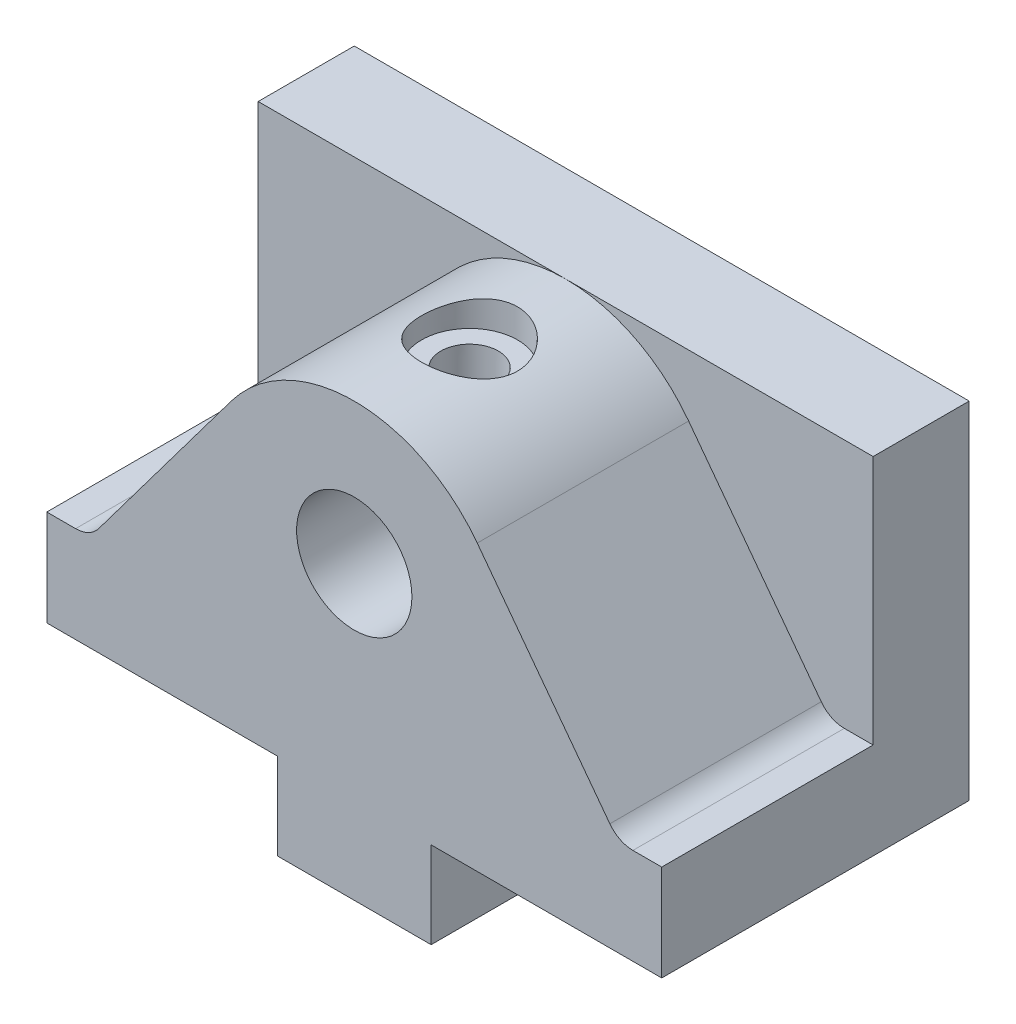
SolidWorks part; units mm, degrees
ref_plane "Front Plane" through (0, 0, 0) normal (0, 0, 1) x (1, 0, 0)
ref_plane "Top Plane" through (0, 0, 0) normal (0, 1, 0) x (1, 0, 0)
ref_plane "Right Plane" through (0, 0, 0) normal (1, 0, 0) x (0, 0, -1)
sketch "Sketch2" plane through (0, 0, 0) normal (0, 1, 0) x (1, 0, 0)
  line L1 (-32, -16) -> (32, -16)
  line L2 (-32, -16) -> (-32, 16)
  line L3 (-32, 16) -> (32, 16)
  line L4 (32, -16) -> (32, 16)
  point P0 (0, 0)
  dimension "D1" = 64
  dimension "D2" = 32
extrude "Boss-Extrude1" add sketch "Sketch2" along normal mid plane 10
sketch "Sketch3" plane through (0, 5, 0) normal (0, 1, 0) x (1, 0, 0)
  line L0 (-32, 16) -> (-32, -16) construction
  line L1 (-32, 16) -> (32, 16)
  line L2 (-32, 16) -> (-32, 6)
  line L3 (-32, 6) -> (32, 6)
  line L4 (32, 16) -> (32, 6)
  line L5 (32, 16) -> (-32, 16) construction
  line L6 (32, -16) -> (32, 16) construction
extrude "Boss-Extrude2" add sketch "Sketch3" along normal blind 36
sketch "Sketch4" plane through (0, 5, 0) normal (0, 1, 0) x (1, 0, 0)
  line L1 (-32, 6) -> (32, 6)
  line L2 (-32, 6) -> (-32, -16)
  line L3 (-32, -16) -> (32, -16)
  line L4 (32, 6) -> (32, -16)
extrude "Boss-Extrude3" add sketch "Sketch4" along normal blind 10
sketch "Sketch5" plane through (0, 0, 16) normal (0, 0, 1) x (1, 0, 0)
  line L0 (-27.5, 15) -> (27.5, 15)
  line L1 (-12.8, 34.6) -> (-27.5, 15)
  line L5 (12.8, 34.6) -> (27.5, 15)
  arc A1 (12.8, 34.6) -> (-12.8, 34.6) centre (0, 25) ccw
  point P4 (0, 15)
  dimension "D2" = 55
extrude "Boss-Extrude4" add sketch "Sketch5" against normal blind 22
sketch "Sketch6" plane through (0, 0, 16) normal (0, 0, 1) x (1, 0, 0)
  line L0 (-32, 5) -> (-32, -5)
  line L2 (-32, 15) -> (-32, -5) construction
  line L3 (-32, 5) -> (-8, 5)
  line L4 (-8, 5) -> (-8, -4)
  line L5 (-8, -4) -> (8, -4)
  line L6 (8, -4) -> (8, 5)
  line L7 (8, 5) -> (32, 5)
  line L8 (32, 15) -> (32, -5) construction
  line L9 (-32, -5) -> (32, -5)
  line L10 (32, -5) -> (32, 5)
extrude "Cut-Extrude1" cut sketch "Sketch6" against normal blind 33
sketch "Sketch7" plane through (0, 0, 16) normal (0, 0, 1) x (1, 0, 0)
  circle A1 centre (0, 26.35) radius 6
extrude "Cut-Extrude2" cut sketch "Sketch7" against normal blind 24
ref_plane "Plane1" through (0, 0, 8) normal (0, 0, 1) x (1, 0, 0)
sketch "Sketch10" plane through (0, 0, 8) normal (0, 0, 1) x (1, 0, 0)
  line L0 (0, -4) -> (0, 13)
  line L1 (8, -4) -> (-8, -4) construction
  line L2 (3, -4) -> (3, 12)
  line L3 (0, -4) -> (3, -4)
  line L4 (0, -4) -> (0, 12) construction
  line L6 (0, 13) -> (3, 12)
  dimension "D1" = 3
revolve "Cut-Revolve2" cut sketch "Sketch10" angle 360 about L0
pattern_linear "LPattern1" count 2 spacing 16 along (0, 0, -1) of "Cut-Revolve2"
ref_plane "Plane2" through (0, 0, 4) normal (0, 0, -1) x (-1, 0, 0)
sketch "Sketch15" plane through (0, 0, 4) normal (0, 0, -1) x (-1, 0, 0)
  line L0 (-0.0036, 30.0115) -> (0, 41)
  line L1 (4.9964, 41.0115) -> (4.9964, 38.0115)
  line L2 (4.9964, 38.0115) -> (2.9964, 38.0115)
  line L3 (-32, 41) -> (32, 41) construction
  line L4 (-0.0036, 30.0115) -> (2.9964, 31.0115)
  line L5 (2.9964, 38.0115) -> (2.9964, 31.0115)
  line L6 (0, 41) -> (4.9964, 41.0115)
revolve "Cut-Revolve4" cut sketch "Sketch15" angle 360 about L0
fillet "Fillet1" radius 3 2 edges at (-27.5, 15, 5) (27.5, 15, 5)
